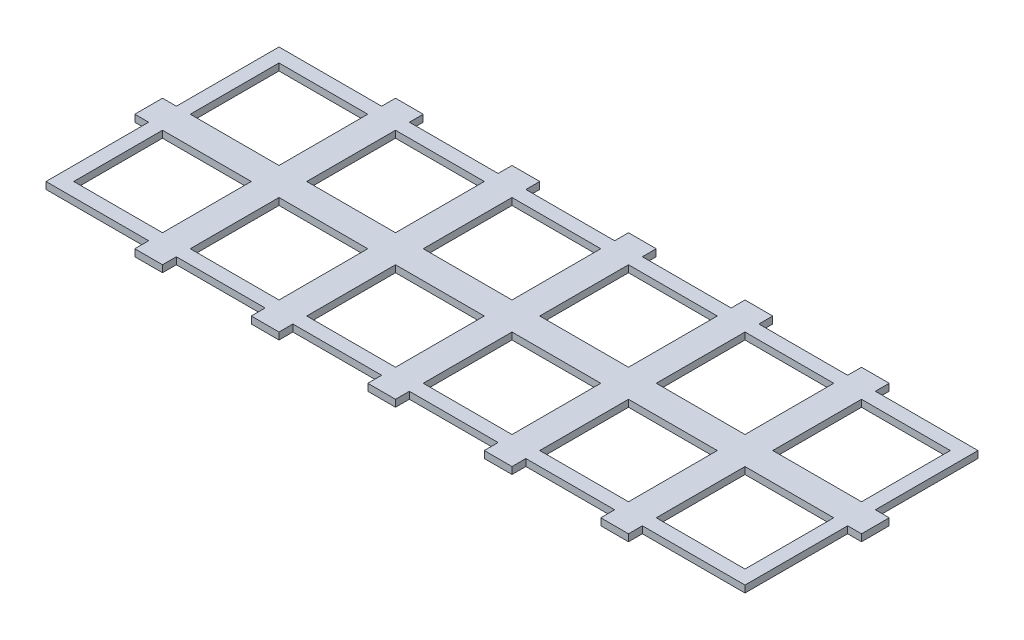
SolidWorks part; units mm, degrees
ref_plane "Alzado" through (0, 0, 0) normal (0, 0, 1) x (1, 0, 0)
ref_plane "Planta" through (0, 0, 0) normal (0, 1, 0) x (1, 0, 0)
ref_plane "Vista lateral" through (0, 0, 0) normal (1, 0, 0) x (0, 0, -1)
sketch "Croquis1" plane through (0, 0, 0) normal (0, 1, 0) x (1, 0, 0)
  line L0 (-10, -10) -> (64, -10)
  line L1 (0, 0) -> (64, 0)
  line L2 (0, 0) -> (0, 64)
  line L3 (0, 64) -> (64, 64)
  line L4 (64, 0) -> (64, 64)
  line L7 (-10, -10) -> (-10, 64)
  line L8 (84, -10) -> (148, -10)
  line L9 (84, 0) -> (148, 0)
  line L10 (84, 0) -> (84, 64)
  line L11 (84, 64) -> (148, 64)
  line L12 (148, 0) -> (148, 64)
  line L16 (168, -10) -> (232, -10)
  line L17 (168, 0) -> (232, 0)
  line L18 (168, 0) -> (168, 64)
  line L19 (168, 64) -> (232, 64)
  line L20 (232, 0) -> (232, 64)
  line L24 (252, -10) -> (316, -10)
  line L25 (252, 0) -> (316, 0)
  line L26 (252, 0) -> (252, 64)
  line L27 (252, 64) -> (316, 64)
  line L28 (316, 0) -> (316, 64)
  line L32 (336, -10) -> (400, -10)
  line L33 (336, 0) -> (400, 0)
  line L34 (336, 0) -> (336, 64)
  line L35 (336, 64) -> (400, 64)
  line L36 (400, 0) -> (400, 64)
  line L40 (420, -10) -> (494, -10)
  line L41 (420, 0) -> (484, 0)
  line L42 (420, 0) -> (420, 64)
  line L43 (420, 64) -> (484, 64)
  line L44 (484, 0) -> (484, 64)
  line L45 (494, -10) -> (494, 64)
  line L49 (84, 84) -> (148, 84)
  line L50 (84, 84) -> (84, 148)
  line L51 (84, 148) -> (148, 148)
  line L52 (148, 84) -> (148, 148)
  line L54 (84, 158) -> (148, 158)
  line L57 (168, 84) -> (232, 84)
  line L58 (168, 84) -> (168, 148)
  line L59 (168, 148) -> (232, 148)
  line L60 (232, 84) -> (232, 148)
  line L62 (168, 158) -> (232, 158)
  line L65 (252, 84) -> (316, 84)
  line L66 (252, 84) -> (252, 148)
  line L67 (252, 148) -> (316, 148)
  line L68 (316, 84) -> (316, 148)
  line L70 (252, 158) -> (316, 158)
  line L73 (336, 84) -> (400, 84)
  line L74 (336, 84) -> (336, 148)
  line L75 (336, 148) -> (400, 148)
  line L76 (400, 84) -> (400, 148)
  line L78 (336, 158) -> (400, 158)
  line L81 (420, 84) -> (484, 84)
  line L82 (420, 84) -> (420, 148)
  line L83 (420, 148) -> (484, 148)
  line L84 (484, 84) -> (484, 148)
  line L85 (494, 84) -> (494, 158)
  line L86 (420, 158) -> (494, 158)
  line L89 (0, 84) -> (64, 84)
  line L90 (0, 84) -> (0, 148)
  line L91 (0, 148) -> (64, 148)
  line L92 (64, 84) -> (64, 148)
  line L94 (-10, 158) -> (64, 158)
  line L95 (-10, 84) -> (-10, 158)
  line L96 (64, 168) -> (84, 168)
  line L97 (504, 84) -> (504, 64)
  line L98 (252, -20) -> (232, -20)
  line L99 (494, 84) -> (504, 84)
  line L100 (494, 64) -> (504, 64)
  line L101 (168, -20) -> (148, -20)
  line L102 (-10, 64) -> (-20, 64)
  line L103 (84, -20) -> (64, -20)
  line L104 (-10, 84) -> (-20, 84)
  line L105 (-20, 84) -> (-20, 64)
  line L118 (64, 168) -> (64, 158)
  line L119 (84, 158) -> (84, 168)
  line L120 (148, 168) -> (148, 158)
  line L121 (168, 158) -> (168, 168)
  line L122 (232, 168) -> (232, 158)
  line L123 (252, 158) -> (252, 168)
  line L124 (316, 168) -> (316, 158)
  line L125 (336, 158) -> (336, 168)
  line L126 (400, 168) -> (400, 158)
  line L127 (420, 158) -> (420, 168)
  line L128 (420, -20) -> (400, -20)
  line L130 (148, -10) -> (148, -20)
  line L131 (168, -20) -> (168, -10)
  line L132 (232, -10) -> (232, -20)
  line L133 (252, -20) -> (252, -10)
  line L134 (316, -10) -> (316, -20)
  line L135 (336, -20) -> (336, -10)
  line L136 (400, -10) -> (400, -20)
  line L137 (420, -20) -> (420, -10)
  line L138 (336, -20) -> (316, -20)
  line L140 (64, -10) -> (64, -20)
  line L141 (84, -20) -> (84, -10)
  line L142 (148, 168) -> (168, 168)
  line L143 (232, 168) -> (252, 168)
  line L144 (316, 168) -> (336, 168)
  line L145 (400, 168) -> (420, 168)
  dimension "D1" = 64
  dimension "D2" = 64
  dimension "D7" = 10
  dimension "D3" = 10
extrude "Saliente-Extruir1" add sketch "Croquis1" along normal blind 5
